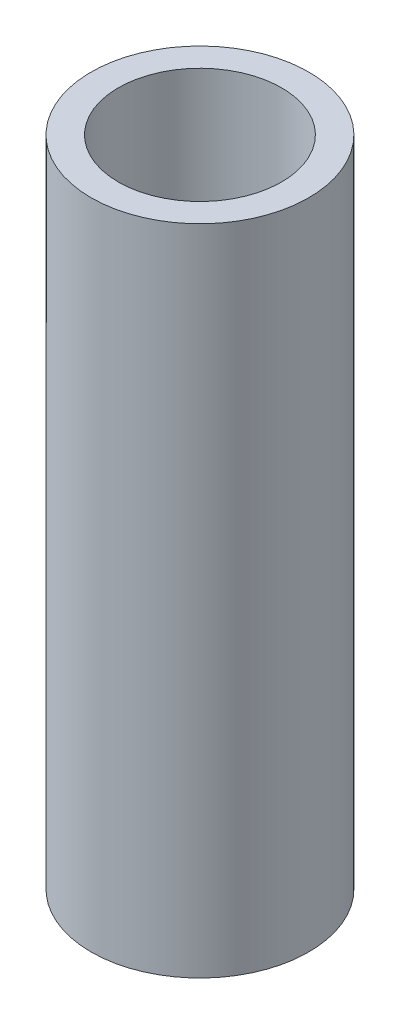
SolidWorks part; units mm, degrees
ref_plane "Front Plane" through (0, 0, 0) normal (0, 0, 1) x (1, 0, 0)
ref_plane "Top Plane" through (0, 0, 0) normal (0, 1, 0) x (1, 0, 0)
ref_plane "Right Plane" through (0, 0, 0) normal (1, 0, 0) x (0, 0, -1)
sketch "Sketch1" plane through (0, 0, 0) normal (0, 1, 0) x (1, 0, 0)
  circle A0 centre (-391.1817, 212.7433) radius 12.7
  circle A1 centre (-391.1817, 212.7433) radius 9.525
  dimension "D1" = 19.05
  dimension "D2" = 25.4
extrude "Boss-Extrude2" add sketch "Sketch1" along normal blind 76.2
